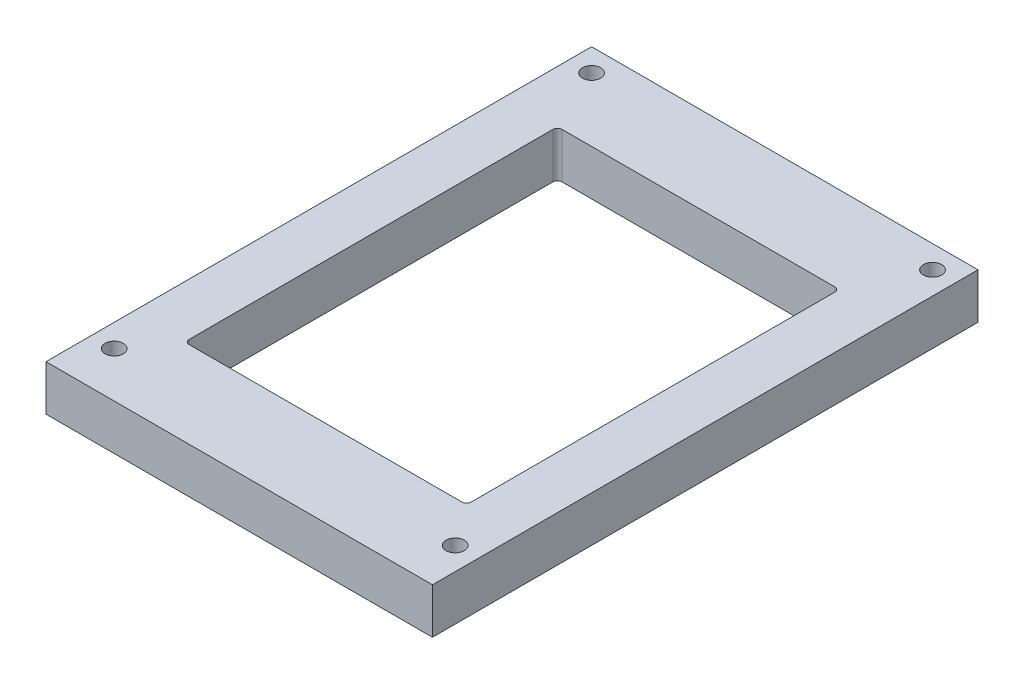
SolidWorks part; units mm, degrees
ref_plane "Front Plane" through (0, 0, 0) normal (0, 0, 1) x (1, 0, 0)
ref_plane "Top Plane" through (0, 0, 0) normal (0, 1, 0) x (1, 0, 0)
ref_plane "Right Plane" through (0, 0, 0) normal (1, 0, 0) x (0, 0, -1)
sketch "Sketch1" plane through (0, 0, 0) normal (0, 1, 0) x (1, 0, 0)
  line L1 (-42.5, -60) -> (42.5, -60)
  line L2 (-42.5, -60) -> (-42.5, 60)
  line L3 (-42.5, 60) -> (42.5, 60)
  line L4 (42.5, -60) -> (42.5, 60)
  line L5 (-42.5, -60) -> (42.5, 60) construction
  line L6 (-42.5, 60) -> (42.5, -60) construction
  point P0 (0, 0)
  dimension "D1" = 120
  dimension "D2" = 85
extrude "Boss-Extrude1" add sketch "Sketch1" along normal blind 10
sketch "Sketch2" plane through (0, 10, 0) normal (0, 1, 0) x (1, 0, 0)
  line L1 (-31, -41) -> (31, -41)
  line L2 (-31, -41) -> (-31, 41)
  line L3 (-31, 41) -> (31, 41)
  line L4 (31, -41) -> (31, 41)
  line L5 (-31, -41) -> (31, 41) construction
  line L6 (-31, 41) -> (31, -41) construction
  point P0 (0, 0)
  dimension "D1" = 82
  dimension "D2" = 62
extrude "Cut-Extrude1" cut sketch "Sketch2" against normal blind 10
fillet "Fillet1" radius 1 4 edges at (31, 5, 41) (-31, 5, 41) (-31, 5, -41) (31, 5, -41)
sketch "Sketch3" plane through (0, 10, 0) normal (0, 1, 0) x (1, 0, 0)
  line L0 (42.5, 60) -> (-42.5, 60) construction
  line L2 (-42.5, 60) -> (-42.5, -60) construction
  line L5 (-42.5, -60) -> (42.5, -60) construction
  line L14 (42.5, -60) -> (42.5, 60) construction
  circle A0 centre (-37.5, -50) radius 2
  circle A2 centre (-37.5, 55) radius 2
  circle A3 centre (37.5, 55) radius 2
  circle A4 centre (37.5, -50) radius 2
  point P36 (0, 50.5)
  point P39 (35.75, 0)
  dimension "D1" = 4
  dimension "D2" = 4
  dimension "D3" = 4
  dimension "D4" = 4
  dimension "D5" = 5
  dimension "D6" = 10
  dimension "D7" = 5
  dimension "D8" = 10
  dimension "D9" = 5
  dimension "D10" = 5
  dimension "D11" = 5
  dimension "D12" = 5
extrude "Cut-Extrude2" cut sketch "Sketch3" against normal blind 5
sketch "Sketch4" plane through (0, 5, 0) normal (0, 1, 0) x (1, 0, 0)
  circle A0 centre (-37.5, -50) radius 1
  circle A1 centre (37.5, -50) radius 1
  circle A2 centre (37.5, 55) radius 1
  circle A3 centre (-37.5, 55) radius 1
  dimension "D1" = 2
  dimension "D2" = 2
  dimension "D3" = 2
  dimension "D4" = 2
extrude "Cut-Extrude3" cut sketch "Sketch4" against normal blind 5
